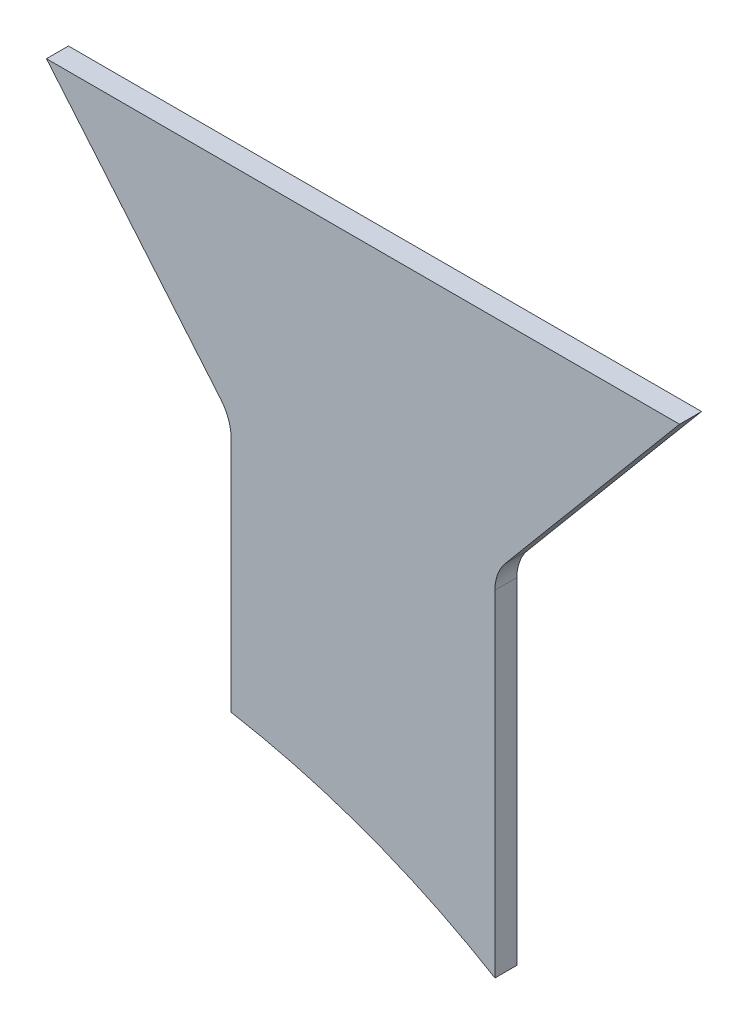
SolidWorks part; units mm, degrees
material "201 Annealed Stainless Steel (SS)"
ref_plane "Front Plane" through (0, 0, 0) normal (0, 0, 1) x (1, 0, 0)
ref_plane "Top Plane" through (0, 0, 0) normal (0, 1, 0) x (1, 0, 0)
ref_plane "Right Plane" through (0, 0, 0) normal (1, 0, 0) x (0, 0, -1)
sketch "Sketch1" plane through (0, 0, 0) normal (0, 0, 1) x (1, 0, 0)
  line L1 (30, 0) -> (30, 80)
  line L2 (30, 80) -> (71.974, 130.0227)
  line L6 (0, 0) -> (30, 0) construction
  line L7 (0, 0) -> (0, 130.0227) construction
  line L8 (-71.974, 130.0227) -> (71.974, 130.0227)
  line L9 (-30, 22.3261) -> (-30, 80)
  line L10 (-30, 80) -> (-71.974, 130.0227)
  line L11 (0, 0) -> (0, -123.071) construction
  line L12 (-60, -150.0833) -> (44.1454, -150.0833) construction
  line L13 (-30, 0) -> (-30, 22.3261) construction
  line L14 (-30, 0) -> (0, 0) construction
  line L15 (-30, 22.3261) -> (-30, -94.1356) construction
  line L16 (30, 0) -> (30, -97.0815) construction
  arc A1 (30, 0) -> (-30, 22.3261) centre (-60, -150.0833) ccw
  circle A2 centre (-60, -150.0833) radius 175 construction
  dimension "D5" = 175
  dimension "D6" = 90
  dimension "D1" = 30
  dimension "D2" = 140
  dimension "D3" = 65.3
  dimension "D4" = 80
extrude "Funnel - Side Panel" add sketch "Sketch1" along normal blind 5
fillet "Fillet1" radius 10 2 edges at (-30, 80, 2.5) (30, 80, 2.5)
